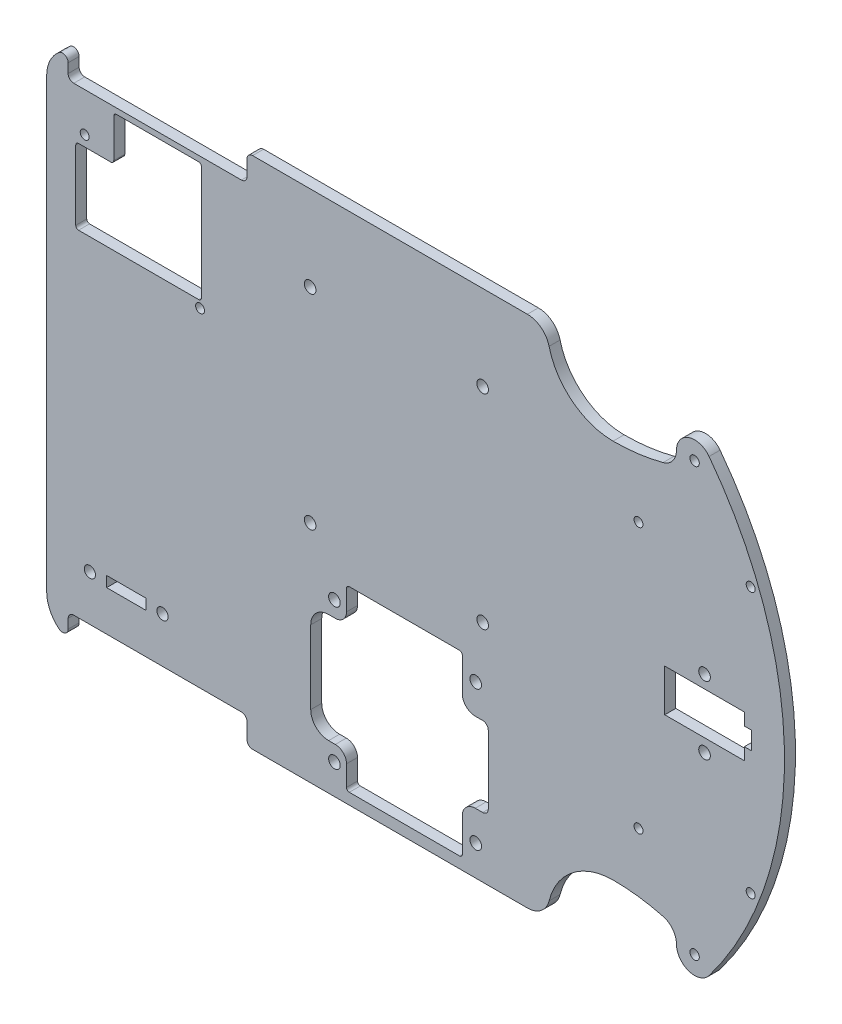
SolidWorks part; units mm, degrees
ref_plane "Alzado" through (0, 0, 0) normal (0, 0, 1) x (1, 0, 0)
ref_plane "Planta" through (0, 0, 0) normal (0, 1, 0) x (1, 0, 0)
ref_plane "Vista lateral" through (0, 0, 0) normal (1, 0, 0) x (0, 0, -1)
sketch "Croquis1" plane through (0, 0, 0) normal (0, 0, 1) x (1, 0, 0)
  line L1 (-104.775, -73.025) -> (104.775, -73.025)
  line L2 (-104.775, -73.025) -> (-104.775, 73.025)
  line L3 (-104.775, 73.025) -> (104.775, 73.025)
  line L4 (104.775, -73.025) -> (104.775, 73.025)
  line L5 (-104.775, -73.025) -> (104.775, 73.025) construction
  line L6 (-104.775, 73.025) -> (104.775, -73.025) construction
  point P0 (0, 0)
  dimension "D1" = 146.05
  dimension "D2" = 209.55
extrude "Saliente-Extruir1" add sketch "Croquis1" along normal blind 3.1242
sketch "Croquis2" plane through (0, 0, 3.1242) normal (0, 0, 1) x (1, 0, 0)
  line L0 (-104.775, -73.025) -> (104.775, -73.025) construction
  line L1 (104.775, 73.025) -> (43.634, 73.025)
  line L2 (104.775, 73.025) -> (104.775, -73.025)
  line L3 (104.775, -73.025) -> (43.634, -73.025)
  line L4 (43.634, 73.025) -> (43.634, -73.025)
  line L5 (0, 0) -> (104.775, 0) construction
  line L6 (69.7976, 73.025) -> (78.6114, 73.025)
  line L7 (69.7976, 73.025) -> (69.7976, 55.6514)
  line L8 (69.7976, 55.6514) -> (78.6114, 55.6514)
  line L9 (78.6114, 73.025) -> (78.6114, 55.6514)
  line L10 (78.6114, -73.025) -> (78.6114, -55.6514)
  line L11 (69.7976, -55.6514) -> (78.6114, -55.6514)
  line L12 (69.7976, -73.025) -> (69.7976, -55.6514)
  line L13 (69.7976, -73.025) -> (78.6114, -73.025)
  circle A0 centre (79.2464, 60.7314) radius 2.921
  circle A1 centre (79.2464, 60.7314) radius 1.3335
  circle A2 centre (79.2464, -60.7314) radius 1.3335
  circle A3 centre (79.2464, -60.7314) radius 2.921
  point P11 (74.2045, 73.025)
  point P12 (74.2045, 55.6514)
  point P13 (79.2464, 57.8104)
  point P14 (82.1674, 60.7314)
  point P28 (82.1674, -60.7314)
  point P29 (79.2464, -57.8104)
  point P30 (74.2045, -55.6514)
  point P31 (74.2045, -73.025)
  point P32 (79.2464, -59.3979)
  point P33 (79.2464, 59.3979)
  point P34 (79.2464, -62.0649)
  point P35 (79.2464, 62.0649)
  dimension "D3" = 5.842
  dimension "D4" = 1.5875
  dimension "D1" = 61.141
  dimension "D2" = 8.8138
  dimension "D5" = 3.556
  dimension "D6" = 17.3736
  dimension "D7" = 118.7958
  dimension "D8" = 118.7958
  dimension "D9" = 124.1298
extrude "Cortar-Extruir1" cut sketch "Croquis2" against normal through all contours L9 A1 | L9 A1 | A2
sketch "Croquis9" plane through (0, 0, 3.1242) normal (0, 0, 1) x (1, 0, 0)
  line L0 (63.3206, 37.6809) -> (95.1722, 37.6809) construction
  line L1 (0, 0) -> (104.775, 0) construction
  line L2 (104.775, -73.025) -> (104.775, 73.025) construction
  line L3 (63.3206, -37.6809) -> (95.1722, -37.6809) construction
  circle A0 centre (63.3206, 37.6809) radius 1.27
  circle A1 centre (95.1722, 37.6809) radius 1.27
  circle A2 centre (95.1722, 37.6809) radius 2.794
  circle A3 centre (79.2464, 60.7314) radius 1.3335 construction
  circle A4 centre (79.2464, 60.7314) radius 1.3335
  circle A5 centre (95.1722, -37.6809) radius 1.27
  circle A6 centre (63.3206, -37.6809) radius 1.27
  point P4 (79.2464, 62.0649)
  point P5 (95.1722, 34.8869)
  point P9 (79.2464, 37.6809)
  point P22 (95.1722, -34.8869)
  point P23 (64.5906, 37.6809)
  point P24 (93.9022, 37.6809)
  dimension "D1" = 29.3116
  dimension "D2" = 2.54
  dimension "D3" = 27.178
  dimension "D4" = 5.588
extrude "Cortar-Extruir6" cut sketch "Croquis9" against normal through all
sketch "Croquis3" plane through (0, 0, 3.1242) normal (0, 0, 1) x (1, 0, 0)
  line L0 (104.775, -73.025) -> (104.775, 73.025) construction
  line L1 (104.775, 73.025) -> (-104.775, 73.025) construction
  line L2 (0, 0) -> (104.775, 0) construction
  line L3 (38.1, 73.025) -> (74.087, 73.025)
  line L4 (38.1, 73.025) -> (38.1, 53.975)
  line L5 (38.1, 53.975) -> (74.087, 53.975)
  line L6 (74.087, 73.025) -> (74.087, 53.975)
  line L7 (74.087, -73.025) -> (74.087, -53.975)
  line L8 (38.1, -53.975) -> (74.087, -53.975)
  line L9 (38.1, -73.025) -> (38.1, -53.975)
  line L10 (38.1, -73.025) -> (74.087, -73.025)
  line L11 (-104.775, -73.025) -> (104.775, -73.025) construction
  line L12 (-95.25, 73.025) -> (0, 73.025)
  line L13 (-104.775, 63.5) -> (-104.775, -63.5)
  line L14 (-95.25, -73.025) -> (0, -73.025)
  line L15 (0, 73.025) -> (0, -73.025)
  circle A0 centre (79.2464, 60.7314) radius 5.1594
  arc A1 (83.3624, 63.8423) -> (83.3624, -63.8423) centre (-1.1052, 0) cw
  arc A2 (74.087, 60.7314) -> (70.3041, 55.8198) centre (69.007, 60.7314) cw
  arc A3 (31.75, 73.025) -> (38.1, 66.675) centre (31.75, 66.675) cw
  arc A4 (37.9138, 68.2015) -> (56.0935, 53.975) centre (56.0935, 72.704) ccw
  arc A5 (37.9138, -68.2015) -> (56.0935, -53.975) centre (56.0935, -72.704) cw
  arc A6 (31.75, -73.025) -> (38.1, -66.675) centre (31.75, -66.675) ccw
  arc A7 (70.3041, -55.8198) -> (56.0935, -53.975) centre (56.0935, -109.6304) ccw
  circle A8 centre (79.2464, -60.7314) radius 5.1594
  arc A9 (-104.775, -63.5) -> (-95.25, -73.025) centre (-95.25, -63.5) ccw
  arc A10 (-95.25, 73.025) -> (-104.775, 63.5) centre (-95.25, 63.5) ccw
  arc A11 (70.3041, 55.8198) -> (56.0935, 53.975) centre (56.0935, 109.6304) cw
  arc A12 (74.087, -60.7314) -> (70.3041, -55.8198) centre (69.007, -60.7314) ccw
  point P48 (-104.775, 73.025)
  point P51 (25.4, 69.2498)
  line M6 (104.775, -73.025) -> (104.775, 73.025)
  line M7 (104.775, 73.025) -> (-104.775, 73.025)
  line M8 (-104.775, 73.025) -> (-104.775, -73.025)
  line M9 (-104.775, -73.025) -> (104.775, -73.025)
  dimension "D1" = 19.05
  dimension "D3" = 6.35
  dimension "D4" = 9.525
  dimension "D5" = 10.3187
  dimension "D6" = 5.08
  dimension "D2" = 38.1
extrude "Cortar-Extruir2" cut sketch "Croquis3" against normal through all contours A3 A4 L4 M7 | A11 A2 L6 L4 A4 M7 | A0 A1 L6 M6 M7 | A1 A8 L7 M9 M6 | L7 A12 A7 A5 L9 M9 | A6 L9 A5 M9 | A10 M7 M8 | A9 M8 M9
sketch "Croquis5" plane through (0, 0, 3.1242) normal (0, 0, 1) x (1, 0, 0)
  line L0 (-95.25, -73.025) -> (31.75, -73.025) construction
  line L1 (-29.7815, -19.2786) -> (20.6375, -19.2786)
  line L2 (-29.7815, -19.2786) -> (-29.7815, -69.85)
  line L3 (-29.7815, -69.85) -> (20.6375, -69.85)
  line L4 (20.6375, -19.2786) -> (20.6375, -69.85)
  line L5 (-29.7815, -44.5643) -> (20.6375, -44.5643) construction
  line L6 (25.4, -63.5) -> (25.4, -62.2144) construction
  line L7 (20.6375, -69.85) -> (13.2715, -69.85)
  line L8 (20.6375, -69.85) -> (20.6375, -19.2786)
  line L9 (20.6375, -19.2786) -> (13.2715, -19.2786)
  line L10 (13.2715, -69.85) -> (13.2715, -19.2786)
  line L11 (-29.7815, -19.2786) -> (-19.6215, -19.2786)
  line L12 (-29.7815, -19.2786) -> (-29.7815, -69.85)
  line L13 (-29.7815, -69.85) -> (-19.6215, -69.85)
  line L14 (-19.6215, -19.2786) -> (-19.6215, -69.85)
  line L15 (13.2715, -33.2486) -> (20.6375, -33.2486)
  line L16 (13.2715, -33.2486) -> (13.2715, -55.88)
  line L17 (13.2715, -55.88) -> (20.6375, -55.88)
  line L18 (20.6375, -33.2486) -> (20.6375, -55.88)
  line L19 (-19.6215, -29.0576) -> (-29.7815, -29.0576)
  line L20 (-19.6215, -29.0576) -> (-19.6215, -60.071)
  line L21 (-19.6215, -60.071) -> (-29.7815, -60.071)
  line L22 (-29.7815, -29.0576) -> (-29.7815, -60.071)
  circle A0 centre (17.0815, -24.7396) radius 1.651
  circle A1 centre (-23.0505, -24.6126) radius 1.651
  circle A2 centre (17.0815, -64.389) radius 1.651
  circle A3 centre (-23.0505, -64.516) radius 1.651
  arc A4 (19.05, -55.88) -> (20.6375, -54.2925) centre (19.05, -54.2925) ccw
  arc A5 (16.9545, -55.88) -> (13.2715, -59.563) centre (16.9545, -59.563) ccw
  arc A6 (-24.7015, -60.071) -> (-29.7815, -54.991) centre (-24.7015, -54.991) cw
  arc A7 (-22.7965, -60.071) -> (-19.6215, -63.246) centre (-22.7965, -63.246) cw
  arc A8 (19.05, -33.2486) -> (20.6375, -34.8361) centre (19.05, -34.8361) cw
  arc A9 (16.9545, -33.2486) -> (13.2715, -29.5656) centre (16.9545, -29.5656) cw
  arc A10 (-24.7015, -29.0576) -> (-29.7815, -34.1376) centre (-24.7015, -34.1376) ccw
  arc A11 (-22.7965, -29.0576) -> (-19.6215, -25.8826) centre (-22.7965, -25.8826) ccw
  arc A12 (-19.6215, -20.0724) -> (-18.8278, -19.2786) centre (-18.8278, -20.0724) cw
  arc A13 (12.4777, -19.2786) -> (13.2715, -20.0724) centre (12.4777, -20.0724) cw
  arc A14 (12.4777, -69.85) -> (13.2715, -69.0563) centre (12.4777, -69.0563) ccw
  arc A15 (-19.6215, -69.0563) -> (-18.8278, -69.85) centre (-18.8278, -69.0563) ccw
  point P4 (18.7325, -24.7396)
  point P5 (17.0815, -23.0886)
  point P6 (-23.0505, -22.9616)
  point P14 (-24.7015, -24.6126)
  dimension "D5" = 3.302
  dimension "D16" = 1.5875
  dimension "D17" = 3.175
  dimension "D18" = 0.7937
  dimension "D1" = 50.5714
  dimension "D2" = 50.419
  dimension "D3" = 3.81
  dimension "D4" = 1.905
  dimension "D6" = 3.175
  dimension "D7" = 4.7625
  dimension "D8" = 5.08
  dimension "D9" = 3.683
  dimension "D10" = 7.366
  dimension "D11" = 10.16
  dimension "D12" = 13.97
  dimension "D13" = 13.97
  dimension "D14" = 9.779
  dimension "D15" = 9.779
extrude "Driver" cut sketch "Croquis5" against normal through all contours L22 L5 L14 L19 A10 | L5 L12 A6 L21 L20 | L14 L5 L16 L10 L1 | L16 L5 L18 A8 L15 | L5 L10 L17 A4 L8 | L5 L20 L14 L3 L10 | A5 L17 L10 | L21 A7 L14 | A11 L19 L14 | L15 A9 L10 | A1 | A3 | A2 | A0
sketch "Croquis6" plane through (0, 0, 3.1242) normal (0, 0, 1) x (1, 0, 0)
  line L0 (-33.45, 19.8814) -> (22.55, 19.8814)
  line L1 (-29.95, 48.8814) -> (19.05, 48.8814)
  line L2 (-29.95, 48.8814) -> (-29.95, -9.1186)
  line L3 (-29.95, -9.1186) -> (19.05, -9.1186)
  line L4 (19.05, 48.8814) -> (19.05, -9.1186)
  line L5 (-18.8278, -19.2786) -> (12.4777, -19.2786) construction
  line L6 (-5.45, -9.1186) -> (-5.45, 74.7014)
  circle A0 centre (-29.95, 48.8814) radius 1.651
  circle A1 centre (19.05, 48.8814) radius 1.651
  circle A2 centre (19.05, -9.1186) radius 1.651
  circle A3 centre (-29.95, -9.1186) radius 1.651
  point P13 (-5.45, 19.8814)
  point P14 (19.05, 19.8814)
  point P16 (-5.45, 48.8814)
  dimension "D1" = 3.302
  dimension "D2" = 58
  dimension "D3" = 49
  dimension "D4" = 56
  dimension "D5" = 6.35
  dimension "D6" = 10.16
  dimension "D7" = 83.82
extrude "RasPi" cut sketch "Croquis6" against normal through all contours A3 | A2 | A1 | A0
sketch "Croquis8" plane through (0, 0, 3.1242) normal (0, 0, 1) x (1, 0, 0)
  line L0 (-93.98, 54.3306) -> (-61.214, 28.0162)
  line L12 (-104.775, 63.5) -> (-104.775, -63.5) construction
  line L13 (-54.4614, 66.3702) -> (-54.4614, -66.3702) construction
  circle A0 centre (-93.98, 54.3306) radius 1.27
  circle A1 centre (-61.214, 28.0162) radius 1.27
  point P2 (-54.4614, 66.3702)
  point P8 (-61.214, 26.7462)
  point P9 (-93.98, 53.0606)
  point P10 (-95.25, 54.3306)
  point P12 (-59.944, 28.0162)
  point P14 (-54.4614, 0)
  dimension "D1" = 13.3096
  dimension "D3" = 2.54
  dimension "D4" = 2.54
  dimension "D2" = 32.766
  dimension "D5" = 9.525
  dimension "D6" = 39.624
  dimension "D7" = 132.7404
extrude "Diferencial trasero" cut sketch "Croquis8" against normal through all contours A0 | A1
sketch "Croquis7" plane through (0, 0, 3.1242) normal (0, 0, 1) x (1, 0, 0)
  line L0 (-82.1901, 33.7483) -> (-82.1901, -50.9778) construction
  line L1 (-87.7464, -50.9778) -> (-76.6339, -50.9778)
  line L2 (-87.7464, -50.9778) -> (-87.7464, -53.975)
  line L3 (-87.7464, -53.975) -> (-76.6339, -53.975)
  line L4 (-76.6339, -50.9778) -> (-76.6339, -53.975)
  line L5 (-95.885, 61.138) -> (-68.4952, 61.138)
  line L6 (-95.885, 61.138) -> (-95.885, 33.7483)
  line L7 (-95.885, 33.7483) -> (-68.4952, 33.7483)
  line L8 (-68.4952, 61.138) -> (-68.4952, 33.7483)
  line L9 (-95.25, -73.025) -> (31.75, -73.025) construction
  circle A0 centre (-71.8714, -52.4764) radius 1.5875
  circle A1 centre (-92.5089, -52.4764) radius 1.5875
  point P16 (-76.6339, -52.4764)
  point P20 (-87.7464, -52.4764)
  dimension "D4" = 3.175
  dimension "D1" = 2.9972
  dimension "D2" = 11.1125
  dimension "D3" = 19.05
  dimension "D5" = 4.7625
extrude "Cortar-Extruir7" cut sketch "Croquis7" against normal through all contours A1 | A0 | L3 L4 L1 L2
sketch "Croquis10" plane through (0, 0, 3.1242) normal (0, 0, 1) x (1, 0, 0)
  line L0 (-104.775, 63.5) -> (-104.775, -63.5) construction
  line L1 (61.3912, -19.4466) -> (54.8894, -19.4466)
  line L2 (61.3912, -19.4466) -> (61.3912, 12.2487)
  line L3 (61.3912, 12.2487) -> (54.8894, 12.2487)
  line L4 (54.8894, -19.4466) -> (54.8894, 12.2487)
  line L5 (61.3912, -19.4466) -> (54.8894, 12.2487) construction
  line L6 (61.3912, 12.2487) -> (54.8894, -19.4466) construction
  line L7 (82.0674, 9.652) -> (82.0674, -9.652) construction
  line L8 (70.7644, -5.9944) -> (93.3704, -5.9944)
  line L9 (70.7644, -5.9944) -> (70.7644, 5.9944)
  line L10 (70.7644, 5.9944) -> (93.3704, 5.9944)
  line L11 (93.3704, -5.9944) -> (93.3704, 5.9944)
  line L12 (70.7644, -5.9944) -> (93.3704, 5.9944) construction
  line L13 (70.7644, 5.9944) -> (93.3704, -5.9944) construction
  line L14 (93.3704, -5.9944) -> (93.3704, 5.9944)
  line L15 (93.3704, 3.1134) -> (93.3704, -1.9666)
  line L16 (82.0674, 9.652) -> (82.0674, -17.272) construction
  line L18 (93.3704, -2.54) -> (95.4024, -2.54)
  line L19 (93.3704, -2.54) -> (93.3704, 2.54)
  line L20 (93.3704, 2.54) -> (95.4024, 2.54)
  line L21 (95.4024, -2.54) -> (95.4024, 2.54)
  circle A0 centre (82.0674, 9.652) radius 1.651
  circle A1 centre (82.0674, -9.652) radius 1.651
  circle A2 centre (82.0674, 9.652) radius 1.651
  point P0 (58.1403, -3.599)
  point P16 (82.0674, 0)
  point P21 (93.3704, 0)
  point P26 (95.4024, 0)
  point P27 (0, 0)
  dimension "D5" = 3.302
  dimension "D1" = 159.6644
  dimension "D2" = 19.304
  dimension "D3" = 22.606
  dimension "D4" = 11.9888
  dimension "D6" = 26.924
  dimension "D7" = 175.5394
  dimension "D8" = 2.032
  dimension "D9" = 5.08
extrude "Cortar-Extruir10" cut sketch "Croquis10" against normal through all contours A0 | L8 L11 L14 L10 L9 | A1 | L18 L21 L20 L14
sketch "Croquis11" plane through (0, 0, 3.1242) normal (0, 0, 1) x (1, 0, 0)
  line L1 (-84.9313, 63.8302) -> (-61.6268, 63.8302)
  line L2 (-85.725, 63.0365) -> (-85.725, 29.9529)
  line L3 (-85.725, 29.9529) -> (-61.6268, 29.9529)
  line L4 (-60.833, 63.0365) -> (-60.833, 30.7467)
  line L5 (-60.833, 29.9529) -> (-95.7263, 29.953)
  line L6 (-60.833, 29.9529) -> (-60.833, 51.289)
  line L7 (-60.833, 51.289) -> (-95.7263, 51.2889)
  line L8 (-96.52, 30.7467) -> (-96.52, 50.4952)
  line L9 (-104.775, 63.5) -> (-104.775, -63.5) construction
  line L10 (31.75, 73.025) -> (-95.25, 73.025) construction
  line L11 (-95.25, 73.025) -> (-57.658, 73.025)
  line L12 (-95.25, 73.025) -> (-95.25, 65.4177)
  line L13 (-95.25, 65.4177) -> (-57.658, 65.4177)
  line L14 (-57.658, 73.025) -> (-57.658, 65.4177)
  line L15 (-46.2915, 73.025) -> (-47.879, 73.025)
  line L16 (-98.679, 80.6323) -> (-47.879, 80.6323)
  line L17 (-98.679, 80.6323) -> (-98.679, 67.0052)
  line L18 (-97.0915, 65.4177) -> (-49.4665, 65.4177)
  line L19 (-47.879, 80.6323) -> (-47.879, 67.0052)
  line L20 (-98.679, 80.6323) -> (-47.879, 65.4177) construction
  line L21 (-98.679, 65.4177) -> (-47.879, 80.6323) construction
  line L22 (0, 0) -> (-104.775, 0) construction
  line L23 (-98.679, -65.4177) -> (-47.879, -80.6323) construction
  line L24 (-98.679, -80.6323) -> (-47.879, -65.4177) construction
  line L25 (-47.879, -80.6323) -> (-47.879, -67.0052)
  line L26 (-97.0915, -65.4177) -> (-49.4665, -65.4177)
  line L27 (-98.679, -80.6323) -> (-98.679, -67.0052)
  line L28 (-98.679, -80.6323) -> (-47.879, -80.6323)
  line L29 (-46.2915, -73.025) -> (-47.879, -73.025)
  line L30 (-57.658, -73.025) -> (-57.658, -65.4177)
  line L31 (-95.25, -65.4177) -> (-57.658, -65.4177)
  line L32 (-95.25, -73.025) -> (-95.25, -65.4177)
  line L33 (-95.25, -73.025) -> (-57.658, -73.025)
  circle A0 centre (-61.214, 28.0162) radius 1.27 construction
  arc A1 (-95.7263, 29.953) -> (-96.52, 30.7467) centre (-95.7263, 30.7467) cw
  arc A2 (-95.7263, 51.2889) -> (-96.52, 50.4952) centre (-95.7263, 50.4952) ccw
  arc A3 (-61.6268, 29.9529) -> (-60.833, 30.7467) centre (-61.6268, 30.7467) ccw
  arc A4 (-61.6268, 63.8302) -> (-60.833, 63.0365) centre (-61.6268, 63.0365) cw
  arc A5 (-84.9313, 63.8302) -> (-85.725, 63.0365) centre (-84.9313, 63.0365) ccw
  arc A6 (-85.725, 52.0827) -> (-86.5188, 51.2889) centre (-86.5188, 52.0827) cw
  circle A7 centre (-93.98, 54.3306) radius 1.27 construction
  circle A8 centre (-93.98, 54.3306) radius 1.27
  arc A9 (-49.4665, 65.4177) -> (-47.879, 67.0052) centre (-49.4665, 67.0052) ccw
  arc A10 (-98.679, 67.0052) -> (-97.0915, 65.4177) centre (-97.0915, 67.0052) ccw
  arc A11 (-47.879, 71.4375) -> (-46.2915, 73.025) centre (-46.2915, 71.4375) cw
  arc A12 (-101.2698, 70.8816) -> (-98.679, 69.6513) centre (-100.2665, 69.6513) cw
  arc A13 (-95.25, 73.025) -> (-104.775, 63.5) centre (-95.25, 63.5) ccw construction
  arc A14 (-95.25, 73.025) -> (-104.775, 63.5) centre (-95.25, 63.5) ccw
  arc A15 (-95.25, -73.025) -> (-104.775, -63.5) centre (-95.25, -63.5) cw
  arc A16 (-101.2698, -70.8816) -> (-98.679, -69.6513) centre (-100.2665, -69.6513) ccw
  arc A17 (-47.879, -71.4375) -> (-46.2915, -73.025) centre (-46.2915, -71.4375) ccw
  arc A18 (-98.679, -67.0052) -> (-97.0915, -65.4177) centre (-97.0915, -67.0052) cw
  arc A19 (-49.4665, -65.4177) -> (-47.879, -67.0052) centre (-49.4665, -67.0052) cw
  point P11 (-61.214, 29.2862)
  point P16 (-96.52, 29.953)
  point P19 (-96.52, 51.2889)
  point P37 (-95.25, 54.3306)
  point P38 (-73.279, 73.025)
  point P46 (-73.279, 63.8302)
  point P91 (-73.279, -73.025)
  dimension "D8" = 0.7937
  dimension "D9" = 1.5875
  dimension "D4" = 3.0417
  dimension "D11" = 50.8
  dimension "D12" = 1.5875
  dimension "D1" = 9.4996
  dimension "D2" = 2.54
  dimension "D3" = 19.05
  dimension "D5" = 21.336
  dimension "D6" = 24.892
  dimension "D7" = 0.6668
  dimension "D10" = 3.175
extrude "Cortar-Extruir11" cut sketch "Croquis11" against normal through all contours L1 A5 L2 L7 L4 A4 | L3 A3 L4 L7 L2 | L7 A2 L8 A1 L5 L2 | L2 A6 L7 | L17 A10 L18 L12 L11 L14 A9 L19 L16 | L14 L11 L12 L13 | L19 A11 L15 | L12 A14 L17 A10 L18 | L17 A14 A12 | A16 A15 L27 | A18 L27 A15 L32 L26 | L32 L33 L30 L26 | A19 L26 L30 L33 A15 L27 L28 L25 | A17 L25 L29
